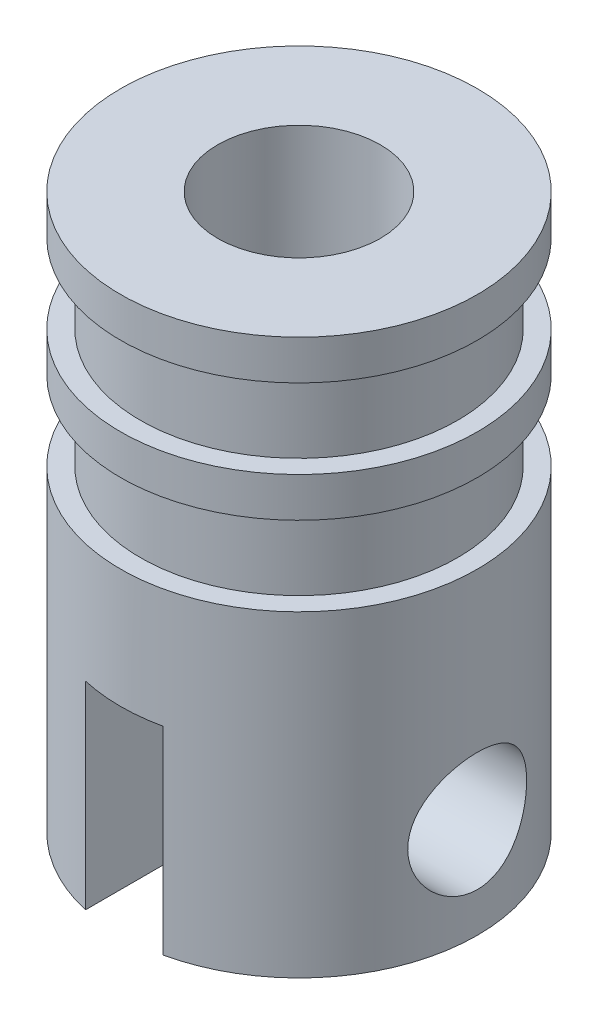
SolidWorks part; units mm, degrees
ref_plane "Alzado" through (0, 0, 0) normal (0, 0, 1) x (1, 0, 0)
ref_plane "Planta" through (0, 0, 0) normal (0, 1, 0) x (1, 0, 0)
ref_plane "Vista lateral" through (0, 0, 0) normal (1, 0, 0) x (0, 0, -1)
sketch "Croquis2" plane through (0, 0, 0) normal (0, 0, 1) x (1, 0, 0)
  line L0 (0, 0) -> (0, 14) construction
  line L1 (0, 14) -> (-4.5, 14)
  line L2 (-4.5, 14) -> (-4.5, 13)
  line L3 (-4.5, 13) -> (-4, 13)
  line L4 (-4, 13) -> (-4, 11)
  line L5 (-4, 11) -> (-4.5, 11)
  line L6 (-4.5, 11) -> (-4.5, 10)
  line L7 (-4.5, 10) -> (-4, 10)
  line L8 (-4, 10) -> (-4, 8)
  line L9 (-4, 8) -> (-4.5, 8)
  line L10 (-4.5, 8) -> (-4.5, 0)
  line L11 (-4.5, 0) -> (0, 0)
  line L12 (0, 0) -> (0, 14)
  dimension "D1" = 14
  dimension "D2" = 4.5
  dimension "D3" = 1
  dimension "D4" = 2
  dimension "D5" = 1
  dimension "D6" = 2
  dimension "D7" = 0.5
  dimension "D8" = 0.5
  dimension "D9" = 0.5
revolve "Revolución4" add sketch "Croquis2" angle 360 about L0
sketch "Croquis3" plane through (0, 0, 0) normal (0, -1, 0) x (1, 0, 0)
  line L0 (0, 4.5) -> (0, -4.5) construction
  line L1 (0, 4.5) -> (-1, 4.5) construction
  line L2 (0, 4.5) -> (0.9672, 4.5) construction
  line L3 (0, 0) -> (-4.5, 0) construction
  line L4 (-4.5, 0) -> (4.5, 0) construction
  line L5 (0, -4.5) -> (0.9672, -4.5) construction
  line L6 (0, -4.5) -> (-1, -4.5) construction
  line L7 (-1, 4.5) -> (-1, -4.5)
  line L8 (-1, -4.5) -> (0.9672, -4.5)
  line L9 (0.9672, -4.5) -> (0.9672, 4.5)
  line L10 (0.9672, 4.5) -> (-1, 4.5)
  circle A0 centre (0, 0) radius 4.5 construction
  dimension "D1" = 1
extrude "Cortar-Extruir1" cut sketch "Croquis3" against normal blind 5
sketch "Croquis4" plane through (0, 14, 0) normal (0, 1, 0) x (1, 0, 0)
  circle A0 centre (0, 0) radius 2.05
extrude "Cortar-Extruir2" cut sketch "Croquis4" against normal blind 9
sketch "Croquis5" plane through (0.9672, 0, 0) normal (-1, 0, 0) x (0, 0, 1)
  circle A0 centre (0, 1.95) radius 0.95
  dimension "D1" = 1.9
sketch "Croquis6" plane through (-1, 0, 0) normal (1, 0, 0) x (0, 0, -1)
  circle A1 centre (0, 1.95) radius 0.95
  dimension "D1" = 1.9
sketch "Croquis7" plane through (0.9672, 0, 0) normal (-1, 0, 0) x (0, 0, 1)
  line L0 (0, 0) -> (0, 1) construction
  line L2 (4.3948, 0) -> (-4.3948, 0) construction
  circle A0 centre (0, 2.5) radius 1.5
  dimension "D1" = 3
  dimension "D2" = 1
extrude "Cortar-Extruir3" cut sketch "Croquis7" against normal through all both and the other way through all
scale "Escala1" scale about centroid uniform scaling yes scale factor 7
